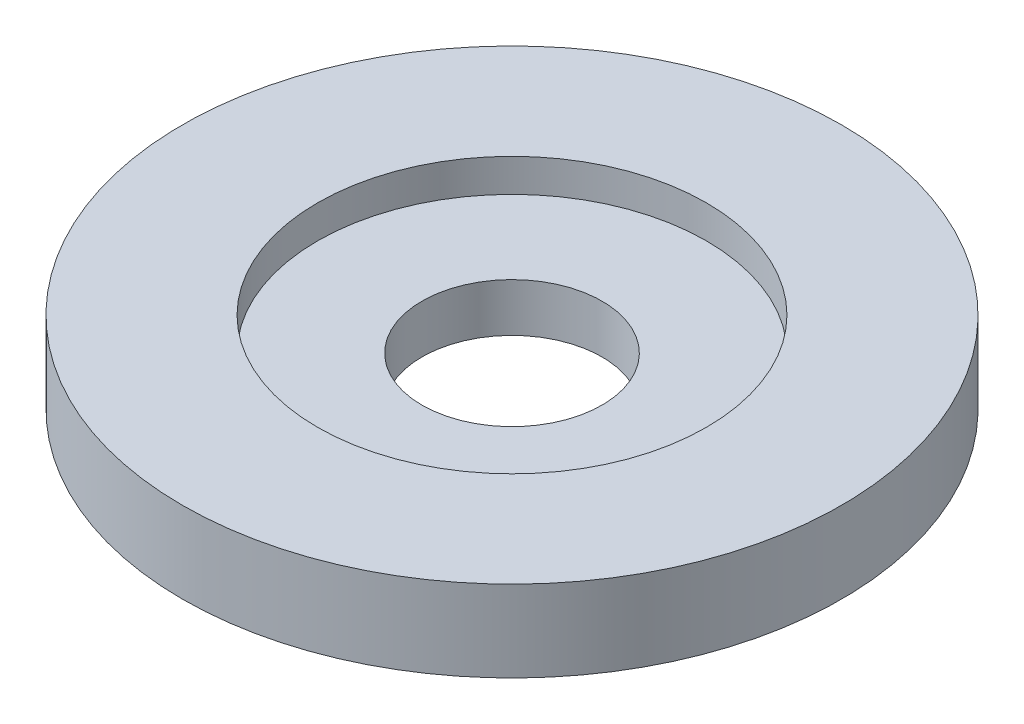
SolidWorks part; units mm, degrees
ref_plane "Front Plane" through (0, 0, 0) normal (0, 0, 1) x (1, 0, 0)
ref_plane "Top Plane" through (0, 0, 0) normal (0, 1, 0) x (1, 0, 0)
ref_plane "Right Plane" through (0, 0, 0) normal (1, 0, 0) x (0, 0, -1)
sketch "Sketch1" plane through (0, 0, 0) normal (0, 1, 0) x (1, 0, 0)
  circle A0 centre (0, 0) radius 19.05
  dimension "D1" = 38.1
extrude "Boss-Extrude1" add sketch "Sketch1" against normal blind 4.699
sketch "Sketch2" plane through (0, 0, 0) normal (0, 1, 0) x (1, 0, 0)
  circle A0 centre (0, 0) radius 11.2395
  dimension "D1" = 22.479
extrude "Cut-Extrude1" cut sketch "Sketch2" against normal blind 1.905 contours A0
sketch "Sketch3" plane through (0, -1.905, 0) normal (0, 1, 0) x (1, 0, 0)
  circle A0 centre (0, 0) radius 5.207
  dimension "D1" = 10.414
extrude "Cut-Extrude2" cut sketch "Sketch3" against normal blind 3.175 contours A0
sketch "Sketch4" plane through (0, -4.699, 0) normal (0, -1, 0) x (1, 0, 0)
  circle A0 centre (0, 0) radius 9.525
  dimension "D1" = 19.05
sketch "Sketch5" plane through (0, 0, 0) normal (0, 1, 0) x (1, 0, 0)
  circle A0 centre (0, 0) radius 15.875
  dimension "D1" = 31.75
sketch "Sketch6" plane through (0, 0, 0) normal (0, 1, 0) x (1, 0, 0)
  circle A0 centre (15.875, 0) radius 0.6863
  circle A1 centre (0, 0) radius 15.875 construction
  circle A2 centre (-15.875, 0) radius 0.5145
sketch "Sketch7" plane through (0, -4.699, 0) normal (0, -1, 0) x (1, 0, 0)
  circle A0 centre (0, 9.525) radius 0.7505
  circle A1 centre (0, 0) radius 9.525 construction
  circle A2 centre (0, -9.525) radius 0.8005
